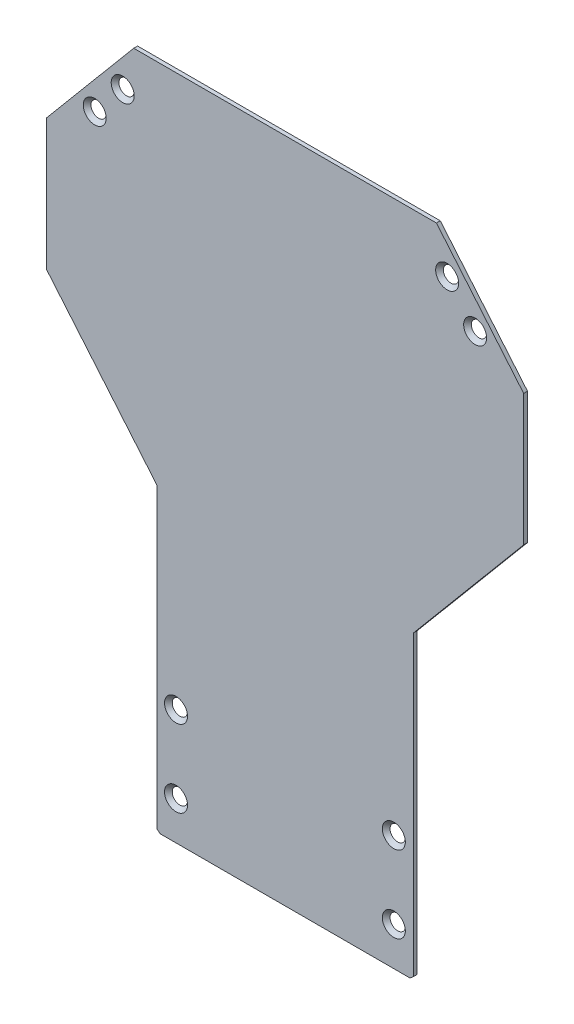
SolidWorks part; units mm, degrees
ref_plane "Plano frontal" through (0, 0, 0) normal (0, 0, 1) x (1, 0, 0)
ref_plane "Plano superior" through (0, 0, 0) normal (0, 1, 0) x (1, 0, 0)
ref_plane "Plano direito" through (0, 0, 0) normal (1, 0, 0) x (0, 0, -1)
sketch "Esboço1" plane through (0, 0, 0) normal (0, 0, 1) x (1, 0, 0)
  line L6 (59.0507, 130.3993) -> (-58.9397, 130.3993)
  line L7 (-58.9397, 130.3993) -> (-92.9445, 89.874)
  line L8 (-92.9445, 89.874) -> (-92.9445, 38.7655)
  line L9 (-92.9445, 38.7655) -> (-49.9445, -12.4799)
  line L10 (-49.9445, -12.4799) -> (-49.9445, -128.493)
  line L11 (-49.9445, -128.493) -> (-48.6244, -129.6007)
  line L12 (-48.6244, -129.6007) -> (48.7354, -129.6007)
  line L13 (50.0555, -128.493) -> (48.7354, -129.6007)
  line L14 (50.0555, -12.4799) -> (50.0555, -128.493)
  line L15 (93.0555, 38.7655) -> (50.0555, -12.4799)
  line L16 (93.0555, 89.874) -> (93.0555, 38.7655)
  line L17 (59.0507, 130.3993) -> (93.0555, 89.874)
  point P16 (0.0555, -129.6007)
  point P17 (0.0555, 130.3993)
  point P18 (0.0555, 120.3993)
  point P19 (0.0555, -119.6007)
extrude "Ressalto-extrusão1" add sketch "Esboço1" along normal blind 1.5
sketch "Esboço2" plane through (0, 0, 1.5) normal (0, 0, 1) x (1, 0, 0)
  line L0 (0, -169.8308) -> (0, 193.4442) construction
  line L1 (-49.9445, -12.4799) -> (-49.9445, -128.493) construction
  line L2 (-58.9397, 130.3993) -> (-92.9445, 89.874) construction
  line L3 (59.0507, 130.3993) -> (-58.9397, 130.3993) construction
  line L6 (-48.6244, -129.6007) -> (48.7354, -129.6007) construction
  circle A0 centre (-42.4445, -114.6007) radius 2
  circle A1 centre (-42.4445, -84.6007) radius 2
  circle A2 centre (-63.2274, 114.3993) radius 2
  circle A3 centre (-74.1357, 101.3993) radius 2
  circle A4 centre (74.1357, 101.3993) radius 2
  circle A5 centre (63.2274, 114.3993) radius 2
  circle A6 centre (42.4445, -84.6007) radius 2
  circle A7 centre (42.4445, -114.6007) radius 2
  dimension "D1" = 7.5
  dimension "D2" = 7.5
  dimension "D3" = 7
  dimension "D4" = 7
  dimension "D5" = 16
  dimension "D6" = 29
  dimension "D7" = 15
  dimension "D8" = 30
hole_wizard "Escareado para parafuso Allen sextavado escareado de M41" positions "3DSketch2" profile "Esboço4" countersink size "M4" standard "ISO" end condition through all
sketch3d "3DSketch2"
  point P0 (-63.2274, 114.3993, 1.5)
  point P3 (-74.1357, 101.3993, 1.5)
  point P6 (63.2274, 114.3993, 1.5)
  point P9 (74.1357, 101.3993, 1.5)
  point P12 (42.4445, -84.6007, 1.5)
  point P15 (42.4445, -114.6007, 1.5)
  point P18 (-42.4445, -114.6007, 1.5)
  point P21 (-42.4445, -84.6007, 1.5)
sketch "Esboço4" plane through (-63.2274, 114.3993, 1.5) normal (1, 0, 0) x (0, -1, 0)
  line L0 (0, 0) -> (0, 1.5)
  line L1 (0, 1.5) -> (2.25, 1.5)
  line L2 (2.25, 1.5) -> (2.25, 2.23)
  line L3 (2.25, 2.23) -> (4.48, 0)
  line L5 (4.48, 0) -> (0, 0)
  line L6 (-2.25, 2.23) -> (-4.48, 0) construction
  line L11 (0, -6.35) -> (0, 107.95) construction
  dimension "Thru Hole Dia." = 4.5
  dimension "Thru Hole Depth" = 1.5
  dimension "Near C'Sink Dia." = 8.96
  dimension "Near C'Sink Angle" = 90
